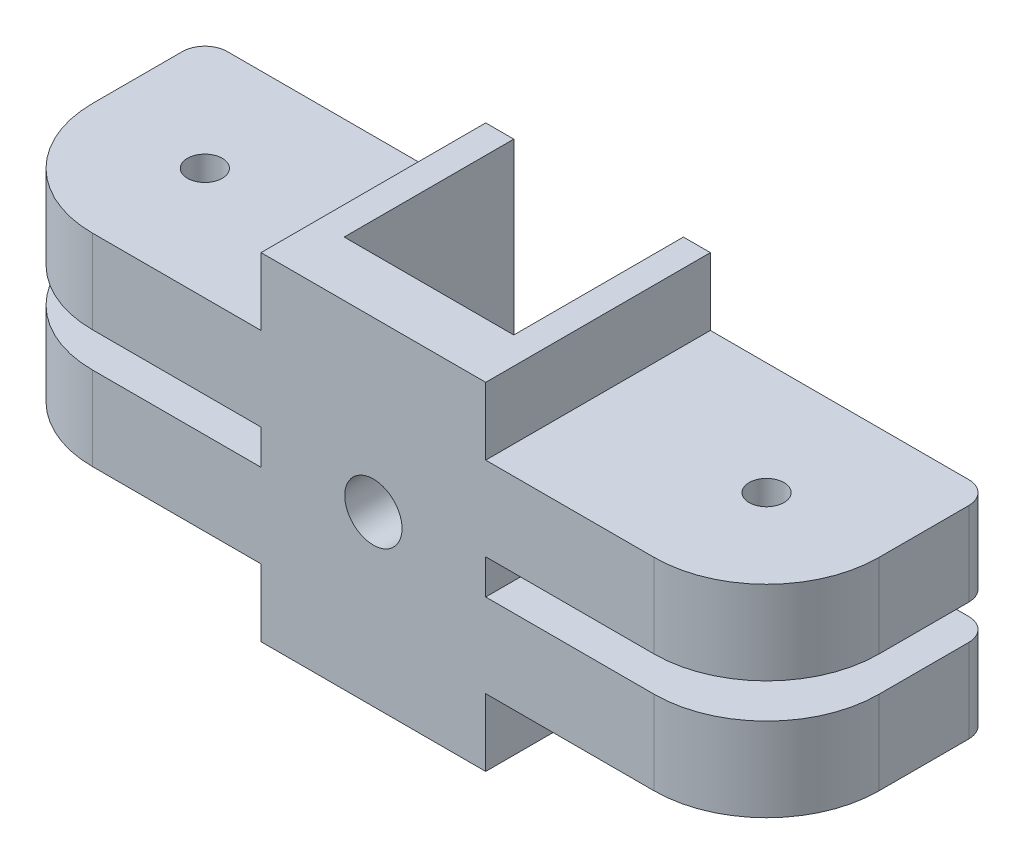
SolidWorks part; units mm, degrees
ref_plane "前视基准面" through (0, 0, 0) normal (0, 0, 1) x (1, 0, 0)
ref_plane "上视基准面" through (0, 0, 0) normal (0, 1, 0) x (1, 0, 0)
ref_plane "右视基准面" through (0, 0, 0) normal (1, 0, 0) x (0, 0, -1)
sketch "草图1" plane through (0, 0, 0) normal (0, 0, 1) x (1, 0, 0)
  line L0 (0, 0) -> (-25, 0) construction
  line L1 (35, 15) -> (-35, 15)
  line L2 (35, 15) -> (35, -15)
  line L3 (35, -15) -> (-35, -15)
  line L5 (35, 15) -> (-35, -15) construction
  line L6 (35, -15) -> (-35, 15) construction
  line L11 (-35, 15) -> (-35, -15)
  line L12 (-35, 1.55) -> (-35, -1.55)
  line L13 (-35, -1.55) -> (-10, -1.55)
  line L14 (-10, -1.55) -> (-10, 1.55)
  line L15 (-10, 1.55) -> (-35, 1.55)
  line L16 (-35, 9) -> (-10, 9)
  line L17 (-10, 9) -> (-10, 15)
  line L18 (-10, 15) -> (-35, 15)
  line L19 (-35, -9) -> (-10, -9)
  line L20 (-10, -9) -> (-10, -15)
  line L21 (0, 15) -> (0, -15) construction
  line L22 (-10, 15) -> (-35, 15)
  line L23 (35, -15) -> (-35, -15)
  line L24 (10, -9) -> (10, -15)
  line L25 (10, 15) -> (35, 15)
  line L26 (35, -9) -> (10, -9)
  line L27 (10, 15) -> (35, 15)
  line L28 (10, 9) -> (10, 15)
  line L29 (35, 9) -> (10, 9)
  line L30 (10, 1.55) -> (35, 1.55)
  line L31 (10, -1.55) -> (10, 1.55)
  line L32 (35, -1.55) -> (10, -1.55)
  line L33 (35, 1.55) -> (35, -1.55)
  line L34 (35, 15) -> (35, -15)
  circle A0 centre (0, 0) radius 2.55
  point P0 (0, 0)
  dimension "D5" = 5.1
  dimension "D1" = 30
  dimension "D2" = 70
  dimension "D3" = 1.55
  dimension "D4" = 6
  dimension "D6" = 25
  dimension "D7" = 25
extrude "凸台-拉伸1" add sketch "草图1" along normal blind 20 contours L2 L32 L31 L30 L29 L28 L1 L17 L16 L11 L15 L14 L13 L19 L20 L23 L24 L26 A0
sketch "草图2" plane through (0, -15, 0) normal (0, -1, 0) x (1, 0, 0)
  line L0 (-7.5, 0) -> (7.6, 0)
  line L1 (7.6, 15.1) -> (-7.5, 15.1)
  line L2 (-7.5, 15.1) -> (-7.5, 0)
  line L3 (7.6, 0) -> (7.6, 15.1)
  line L4 (-10, 20) -> (-10, 0) construction
  line L5 (10, 0) -> (-10, 0) construction
  dimension "D1" = 15.1
  dimension "D2" = 15.1
  dimension "D3" = 2.5
extrude "切除-拉伸1" cut sketch "草图2" against normal up to next
sketch "草图3" plane through (0, 9, 0) normal (0, 1, 0) x (1, 0, 0)
  line L0 (35, 0) -> (10, 0) construction
  line L2 (35, -20) -> (35, 0) construction
  circle A0 centre (25, -10) radius 1.55
  dimension "D3" = 3.1
  dimension "D1" = 10
  dimension "D2" = 10
extrude "切除-拉伸2" cut sketch "草图3" against normal blind 100
mirror "镜向1" about plane through (0, 0, 0) normal (1, 0, 0) of "切除-拉伸2"
fillet "圆角1" radius 2 4 edges at (35, 5.275, 0) (35, -5.275, 0) (-35, 5.275, 0) (-35, -5.275, 0)
fillet "圆角2" radius 10 4 edges at (35, -5.275, 20) (35, 5.275, 20) (-35, -5.275, 20) (-35, 5.275, 20)
